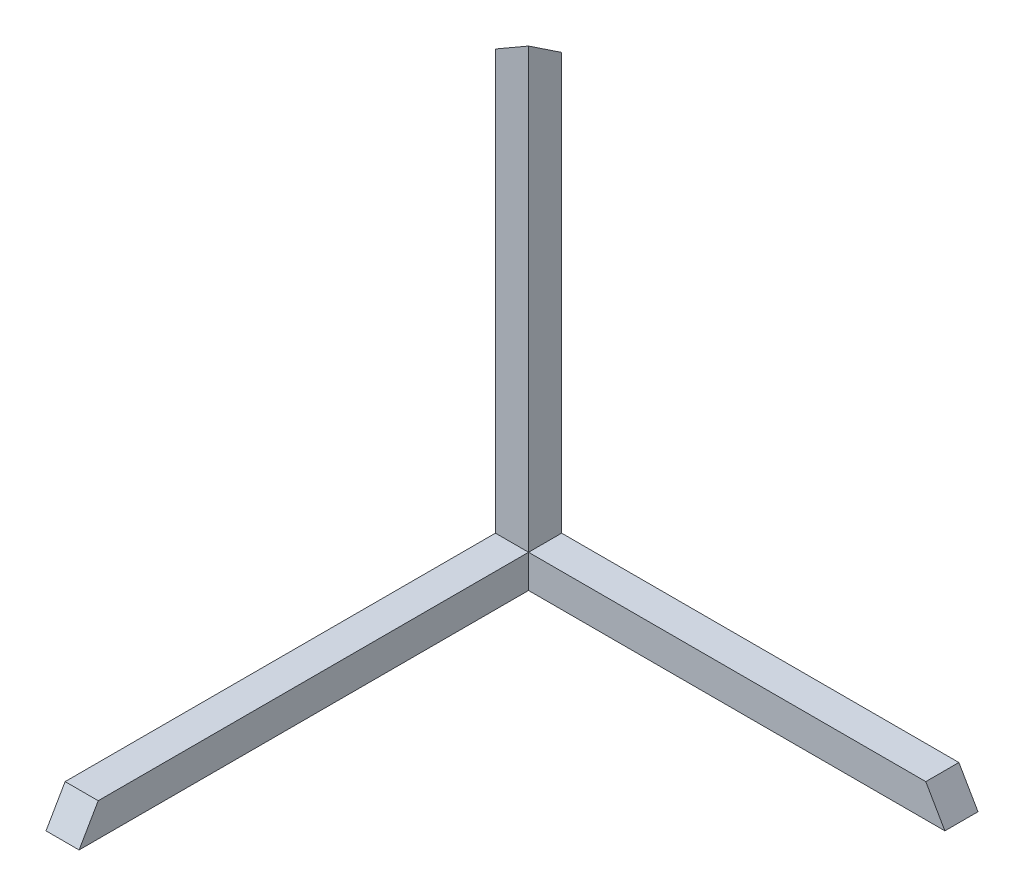
SolidWorks part; units mm, degrees
ref_plane "Front Plane" through (0, 0, 0) normal (0, 0, 1) x (1, 0, 0)
ref_plane "Top Plane" through (0, 0, 0) normal (0, 1, 0) x (1, 0, 0)
ref_plane "Right Plane" through (0, 0, 0) normal (1, 0, 0) x (0, 0, -1)
sketch "Sketch1" plane through (0, 0, 0) normal (0, 0, 1) x (1, 0, 0)
  line L1 (-77.5074, 22.3679) -> (-72.5074, 22.3679)
  line L2 (-77.5074, 22.3679) -> (-77.5074, -42.6321)
  line L3 (-77.5074, -42.6321) -> (-72.5074, -42.6321)
  line L4 (-72.5074, 22.3679) -> (-72.5074, -42.6321)
  dimension "D1" = 65
  dimension "D2" = 5
extrude "Boss-Extrude1" add sketch "Sketch1" along normal blind 5
sketch "Sketch2" plane through (-77.5074, 0, 0) normal (-1, 0, 0) x (0, 0, 1)
  line L0 (5, 22.3679) -> (5, -42.6321) construction
  line L1 (5, -42.6321) -> (70, -42.6321)
  line L2 (5, -42.6321) -> (5, -37.6321)
  line L3 (5, -37.6321) -> (70, -37.6321)
  line L4 (70, -42.6321) -> (70, -37.6321)
  dimension "D1" = 5
  dimension "D2" = 65
sketch "Sketch3" plane through (0, 0, 5) normal (0, 0, 1) x (1, 0, 0)
extrude "Boss-Extrude3" add sketch "Sketch2" against normal blind 5 contours L3 L4 L1 L2
sketch "Sketch4" plane through (0, -37.6321, 0) normal (0, 1, 0) x (1, 0, 0)
  line L1 (-77.5074, 0) -> (-12.5074, 0)
  line L2 (-77.5074, 0) -> (-77.5074, -5)
  line L3 (-77.5074, -5) -> (-12.5074, -5)
  line L4 (-12.5074, 0) -> (-12.5074, -5)
  dimension "D1" = 5
  dimension "D2" = 65
extrude "Boss-Extrude4" add sketch "Sketch4" against normal blind 5
draft "Draft3" type of draft neutral plane draft angle 30 faces to draft 1 face at (-12.5074, -40.1321, 2.5) neutral plane through (0, -37.6321, 0) neutral plane normal (0, 1, 0) parameters "D1"=30
draft "Draft4" type of draft neutral plane draft angle 30 faces to draft 1 face at (-11.0641, -40.1321, 2.5) neutral plane through (0, -37.6321, 0) neutral plane normal (0, 1, 0) parameters "D1"=30
draft "Draft7" type of draft neutral plane draft angle 30 faces to draft 1 face at (-75.0074, -40.1321, 70) neutral plane through (-72.5074, -37.6321, 5) neutral plane normal (0, 1, 0) parameters "D1"=30
draft "Draft8" type of draft neutral plane draft angle 30 faces to draft 1 face at (-75.0074, 22.3679, 2.5) neutral plane through (-77.5074, 22.3679, 5) neutral plane normal (-1, 0, 0) parameters "D1"=30
draft "Draft9" type of draft neutral plane draft angle 30 faces to draft 1 face at (-75.0074, 23.8113, 2.5) neutral plane through (0, 0, 0) neutral plane normal (0, 0, -1) parameters "D1"=30
sketch "Sketch5" plane through (-72.5074, 0, 0) normal (1, 0, 0) x (0, 0, -1)
  text T0 "Y" font "Consolas" height 3.175
  text T1 "Z"
